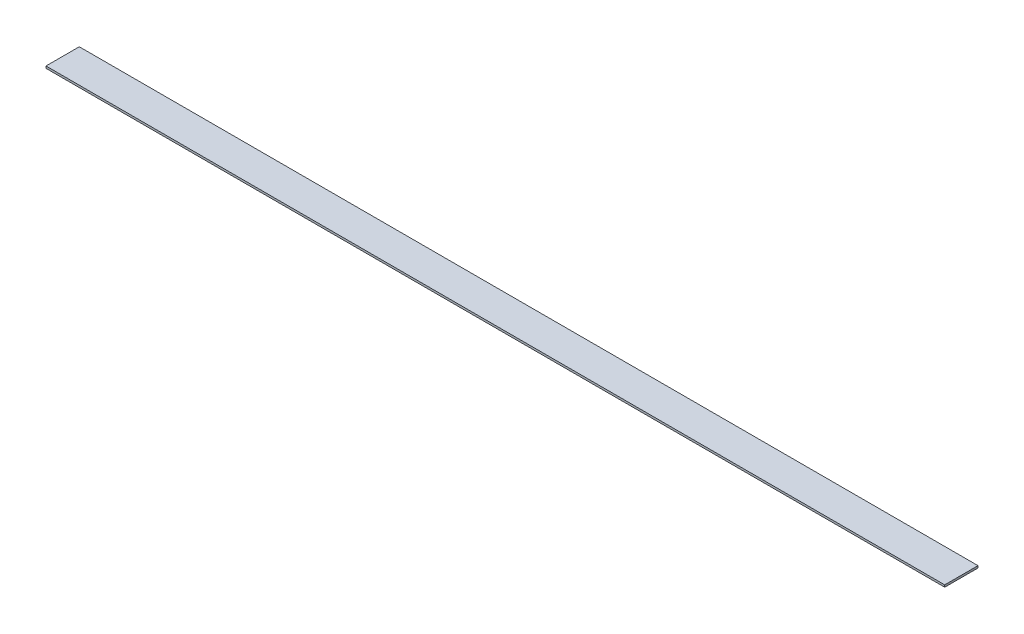
SolidWorks part; units mm, degrees
ref_plane "Front Plane" through (0, 0, 0) normal (0, 0, 1) x (1, 0, 0)
ref_plane "Top Plane" through (0, 0, 0) normal (0, 1, 0) x (1, 0, 0)
ref_plane "Right Plane" through (0, 0, 0) normal (1, 0, 0) x (0, 0, -1)
sketch "Sketch1" plane through (0, 0, 0) normal (0, 1, 0) x (1, 0, 0)
  line L1 (-342.9, 12.7) -> (342.9, 12.7)
  line L2 (-342.9, 12.7) -> (-342.9, -12.7)
  line L3 (-342.9, -12.7) -> (342.9, -12.7)
  line L4 (342.9, 12.7) -> (342.9, -12.7)
  line L5 (-342.9, 12.7) -> (342.9, -12.7) construction
  line L6 (-342.9, -12.7) -> (342.9, 12.7) construction
  point P0 (0, 0)
  dimension "D1" = 25.4
  dimension "D2" = 685.8
extrude "Boss-Extrude1" add sketch "Sketch1" along normal blind 1.5875
